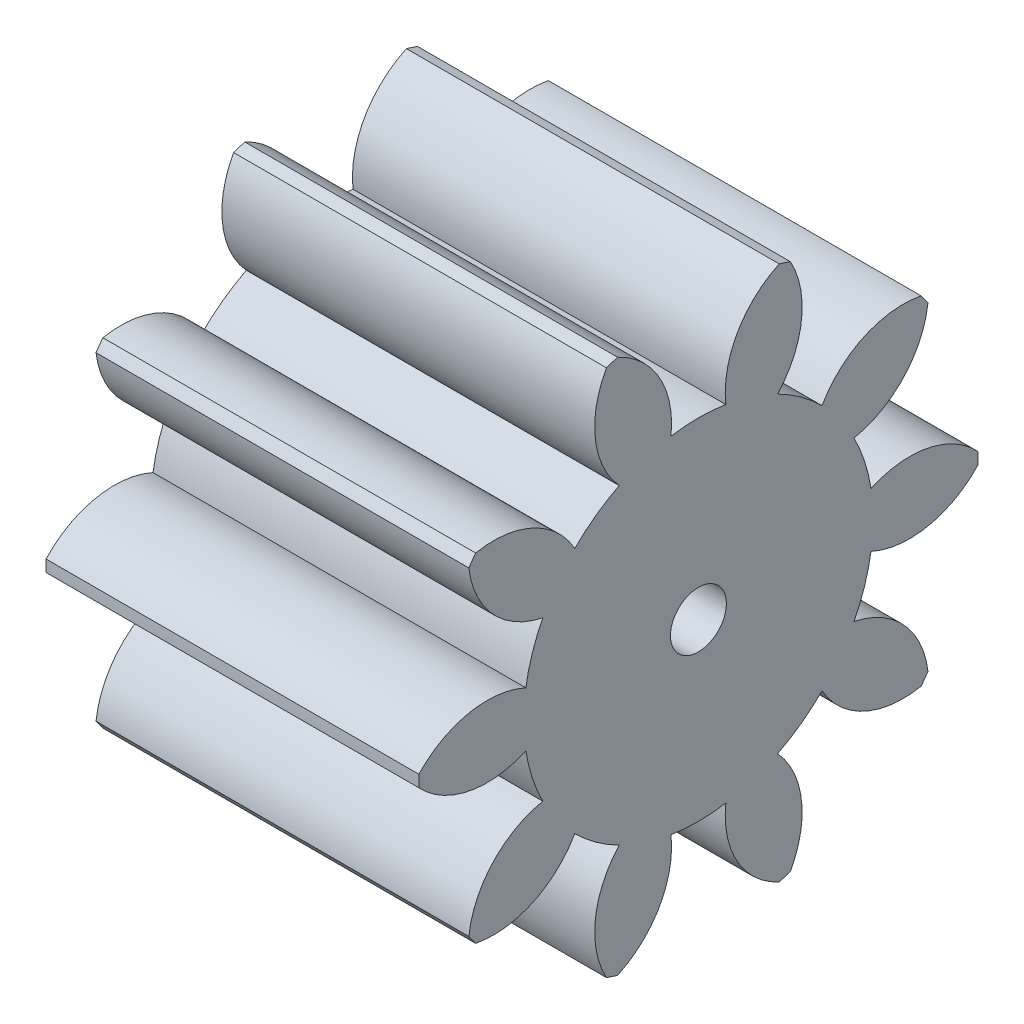
SolidWorks part; units mm, degrees
ref_plane "Plane1" through (0, 0, 0) normal (0, 0, 1) x (1, 0, 0)
ref_plane "Plane2" through (0, 0, 0) normal (0, 1, 0) x (1, 0, 0)
ref_plane "Plane3" through (0, 0, 0) normal (1, 0, 0) x (0, 0, -1)
sketch "HoldingSke" plane through (0, 0, 0) normal (0, 1, 0) x (1, 0, 0)
  line L0 (0, 0) -> (0.3939, -0.0695)
  line L1 (-15, 0) -> (100, 0) construction
  line L2 (0, 0) -> (-2.1039, 2.3779)
  line L3 (0, 0) -> (-11.863, 4.5341)
  line L4 (0, 0) -> (8.5048, 1.4996)
  line L5 (0, 0) -> (-46.8476, -17.4728)
  line L6 (0, 0) -> (-16.5793, -11.1861)
  line L7 (-2.1039, 2.3779) -> (8.6586, 51.2059)
  line L8 (-76.2, 54.61) -> (-75.7, 54.61)
  line L9 (-71.009, 38.7566) -> (-53.1078, 45.2721)
  line L10 (-76.2, 71.12) -> (104.1128, 71.12)
  line L11 (0, 0) -> (-20, 0)
  line L12 (-76.2, 101.6) -> (-76.113, 101.6)
  line L13 (24.9733, 27.94) -> (52.9518, 28.4284)
  line L14 (24.9733, 27.94) -> (24.9743, 27.94)
  line L15 (24.9733, 27.94) -> (100.4006, 29.5858)
  line L16 (-63.627, -2.5) -> (-12.827, -2.5)
  circle A0 centre (0, 0) radius 1.5
  circle A1 centre (0, 0) radius 9.374
  circle A2 centre (0, 0) radius 37.5
  circle A3 centre (0, 0) radius 1.5
  dimension "MHD" = 18.748
  dimension "Hub_dia" = 75
  dimension "Bore" = 3
  dimension "MBD" = 3
  dimension "Num_teeth" = 10
  dimension "Pitch" = 0.4
  dimension "Overall_len" = 50
  dimension "Show_teeth" = 10
  dimension "Thickness" = 20
  dimension "OAL" = 50.0001
  dimension "T_dim" = 0.5
  dimension "Ap" = 20
  dimension "H" = 19.05
  dimension "Pitch_radius" = 180.3128
  dimension "Width" = 20
  dimension "Backlash" = 0.087
  dimension "Addendum_fac" = 1
  dimension "Dedendum_fac" = 1.25
  dimension "Clearance_fac" = 0.25
  dimension "Dedendum_add" = 0.001
  dimension "Module" = 2.5
sketch "BasProSke" plane through (0, 0, 0) normal (0, 1, 0) x (1, 0, 0)
  line L0 (-10, 0) -> (60, 0) construction
  line L1 (0, 0) -> (0, 15)
  line L2 (0, 0) -> (20, 0)
  line L3 (20, 0) -> (20, 15)
  line L4 (20, 15) -> (0, 15)
  dimension "Thickness" = 20
  dimension "Diameter" = 30
revolve "Base-Revolve" add sketch "BasProSke" angle 360 about L0
sketch "TooCutSke" plane through (0, 0, 0) normal (1, 0, 0) x (0, 0, -1)
  line L1 (0, 0) -> (0, 107) construction
  line L2 (0, 0) -> (-2.1074, 12.3211) construction
  line L3 (0, 0) -> (-7.6446, 23.5277) construction
  line L4 (-2.1074, 12.3211) -> (-3.8223, 11.7639) construction
  arc A0 (1.4713, 9.2578) -> (-1.4713, 9.2578) centre (0, 0) ccw
  arc A1 (4.3702, 14.3758) -> (-4.3702, 14.3758) centre (0, 0) ccw
  circle A2 centre (0, 0) radius 12.5 construction
  circle A3 centre (0, 0) radius 11.7462 construction
  arc A4 (-1.4713, 9.2578) -> (-4.3702, 14.3758) centre (-6.4392, 9.8239) ccw
  arc A5 (4.3702, 14.3758) -> (1.4713, 9.2578) centre (6.4392, 9.8239) ccw
  dimension "Root_dia" = 18.748
  dimension "Overcut_dia" = 30.0508
  dimension "Pitch_dia" = 25
  dimension "Base_dia" = 23.4923
  dimension "Flank_rad" = 5
  dimension "Half_ang" = 18
  dimension "Half_CT" = 1.8032
extrude "ToothCut" cut sketch "TooCutSke" along normal through all
fillet "Breaks" [suppressed] radius 0.05
fillet "RootFillets" [suppressed] radius 0.626
pattern_circular "TeethCuts" count 10 every 36 about axis through (-10, 0, 0) along (1, 0, 0) of "ToothCut", "RootFillets", "Breaks"
sketch "HubNeaOneSke" plane through (0, 0, 0) normal (-1, 0, 0) x (0, 0, 1)
  circle A0 centre (0, 0) radius 9.374
  dimension "Diameter" = 18.748
extrude "HubNearOne" [suppressed] add sketch "HubNeaOneSke" along normal blind 30.0001
sketch "HubNeaBotSke" plane through (0, 0, 0) normal (-1, 0, 0) x (0, 0, 1)
  circle A0 centre (0, 0) radius 9.374
  dimension "Diameter" = 18.748
extrude "HubNearBoth" [suppressed] add sketch "HubNeaBotSke" along normal blind 15
ref_plane "FarPln" through (20, 0, 0) normal (1, 0, 0) x (0, 0, -1)
sketch "HubFarSke" plane through (20, 0, 0) normal (1, 0, 0) x (0, 0, -1)
  circle A0 centre (0, 0) radius 9.374
  dimension "Diameter" = 18.748
extrude "HubFar" [suppressed] add sketch "HubFarSke" along normal blind 15
sketch "BorSke" plane through (0, 0, 0) normal (1, 0, 0) x (0, 0, -1)
  circle A0 centre (0, 0) radius 1.5
  dimension "Diameter" = 3
extrude "Bore" cut sketch "BorSke" along normal mid plane 100.0001
sketch "KeySke" plane through (0, 0, 0) normal (1, 0, 0) x (0, 0, -1)
  line L0 (-0.6, 0) -> (-0.6, 2)
  line L1 (-0.6, 2) -> (0.6, 2)
  line L2 (0.6, 2) -> (0.6, 0)
  line L3 (0, 0) -> (0, 34) construction
  line L4 (-0.6, 0) -> (0.6, 0)
  dimension "Offset" = 2
  dimension "Width" = 1.2
extrude "Keyway" [suppressed] cut sketch "KeySke" along normal mid plane 100.0001
pattern_circular "Keyway2" [suppressed] count 2 every 90 about axis through (-10, 0, 0) along (1, 0, 0)
equation "' \"Module@HoldingSke\" = 6.35"
equation "' \"Num_teeth@HoldingSke\" = 12"
equation "' \"Ap@HoldingSke\" =  20"
equation "' \"Ap@HoldingSke\" = 20"
equation "' \"Width@HoldingSke\" = 0.5 * 25.4"
equation "' \"Hub_dia@HoldingSke\"= 1 * 25.4"
equation "' \"Hub_dia@HoldingSke\" = 1 * 25.4"
equation "' \"Overall_len@HoldingSke\" = 1.0 * 25.4"
equation "' \"Bore@HoldingSke\" = 0.75 * 25.4"
equation "' \"T_dim@HoldingSke\" = 0.1 * 25.4"
equation "' \"Width@KeySke\" = 0.25 * 25.4"
equation "' \"Show_teeth@HoldingSke\" = 13"
equation "' \"Backlash@HoldingSke\" = 0.009 * 25.4"
equation "' \"Addendum_fac@HoldingSke\" = 1.0"
equation "' \"Dedendum_fac@HoldingSke\" = 1.25"
equation "' \"Dedendum_add@HoldingSke\" = 0.00005 * 25.4"
equation "' \"Clearance_fac@HoldingSke\" = 0.25"
equation "\"Pitch@HoldingSke\" = 1 / \"Module@HoldingSke\""
equation "\"Overcut_dia@TooCutSke\" = (\"Num_teeth@HoldingSke\" + 2 * \"Addendum_fac@HoldingSke\") / \"Pitch@HoldingSke\" + 0.002 * 25.4"
equation "\"Pitch_dia@TooCutSke\" = \"Num_teeth@HoldingSke\" / \"Pitch@HoldingSke\""
equation "\"Base_dia@TooCutSke\" = \"Num_teeth@HoldingSke\" / \"Pitch@HoldingSke\" * cos((\"Ap@HoldingSke\"  * 3.14159265 / 180))"
equation "\"Root_dia@TooCutSke\" = (\"Num_teeth@HoldingSke\" + 2) / \"Pitch@HoldingSke\" - 2 * (\"Addendum_fac@HoldingSke\" + \"Dedendum_fac@HoldingSke\") / \"Pitch@HoldingSke\" - \"Dedendum_add@HoldingSke\" * 2"
equation "\"Half_ang@TooCutSke\" = 180 / \"Num_teeth@HoldingSke\""
equation "\"Half_CT@TooCutSke\" = \"Num_teeth@HoldingSke\" / \"Pitch@HoldingSke\" * sin((3.14159265 / 2 / \"Num_teeth@HoldingSke\")) / 2 - 7 * \"Backlash@HoldingSke\" / 4"
equation "\"Flank_rad@TooCutSke\" = \"Num_teeth@HoldingSke\" / \"Pitch@HoldingSke\" / 5"
equation "\"Radius@RootFillets\" = \"Clearance_fac@HoldingSke\" / \"Pitch@HoldingSke\" + \"Dedendum_add@HoldingSke\""
equation "\"Break_rad@Breaks\" = 0.02 / \"Pitch@HoldingSke\""
equation "\"Thickness@HoldingSke\" = \"Width@HoldingSke\""
equation "\"OAL@HoldingSke\" = \"Thickness@HoldingSke\""
equation "\"MHD@HoldingSke\" = (\"Num_teeth@HoldingSke\" + 2) / \"Pitch@HoldingSke\" - 2 * (\"Addendum_fac@HoldingSke\" + \"Dedendum_fac@HoldingSke\")  / \"Pitch@HoldingSke\" - \"Dedendum_add@HoldingSke\" * 2"
equation "\"MBD@HoldingSke\" = (\"Num_teeth@HoldingSke\" + 2) / \"Pitch@HoldingSke\" - 2 * (\"Addendum_fac@HoldingSke\" + \"Dedendum_fac@HoldingSke\")  / \"Pitch@HoldingSke\" - \"Dedendum_add@HoldingSke\" * 2 - 0.002 * 25.4"
equation "\"MHD@HoldingSke\" = ((sgn( \"MHD@HoldingSke\" - \"Hub_dia@HoldingSke\" )-1)*( \"MHD@HoldingSke\" - \"Hub_dia@HoldingSke\" ))/-2+ \"Hub_dia@HoldingSke\""
equation "\"MBD@HoldingSke\" = ((sgn( \"MBD@HoldingSke\" - \"Bore@HoldingSke\" )-1)*( \"MBD@HoldingSke\" - \"Bore@HoldingSke\" ))/-2+ \"Bore@HoldingSke\""
equation "\"OAL@HoldingSke\" = ((sgn( \"OAL@HoldingSke\" - \"Overall_len@HoldingSke\" )+1)*( \"OAL@HoldingSke\" - \"Overall_len@HoldingSke\" ))/2 + \"Overall_len@HoldingSke\" + 0.000002 * 25.4"
equation "\"Num_teeth@TeethCuts\" = int( \"Show_teeth@HoldingSke\" ) + 1"
equation "\"Num_teeth@TeethCuts\" = ((sgn( \"Num_teeth@TeethCuts\" - \"Num_teeth@HoldingSke\" )-1)*( \"Num_teeth@TeethCuts\" - \"Num_teeth@HoldingSke\" ))/-2+ \"Num_teeth@HoldingSke\""
equation "\"Num_teeth@TeethCuts\" = ((sgn( \"Num_teeth@TeethCuts\" - 2.0)+1)*( \"Num_teeth@TeethCuts\" - 2.0))/2 +2.0"
equation "\"Angle@TeethCuts\" = 360.0 / \"Num_teeth@HoldingSke\""
equation "\"Diameter@BasProSke\" = (\"Num_teeth@HoldingSke\" + 2 * \"Addendum_fac@HoldingSke\") / \"Pitch@HoldingSke\""
equation "\"Thickness@BasProSke\"  = \"Thickness@HoldingSke\""
equation "' \"Fillet_rad@BasProSke\" =  \"Thickness@HoldingSke\" * 0.05"
equation "' \"Fillet_rad@BasProSke\" = \"Thickness@HoldingSke\" * 0.05"
equation "\"MHD@HoldingSke\" = ((sgn( \"MHD@HoldingSke\" - \"Root_dia@TooCutSke\" )-1)*( \"MHD@HoldingSke\" - \"Root_dia@TooCutSke\" ))/-2+ \"Root_dia@TooCutSke\""
equation "\"Diameter@HubNeaOneSke\" = \"MHD@HoldingSke\""
equation "\"Length@HubNearOne\" = \"OAL@HoldingSke\" - \"Thickness@BasProSke\""
equation "\"Diameter@HubNeaBotSke\" = \"MHD@HoldingSke\""
equation "\"Length@HubNearBoth\" = ( \"OAL@HoldingSke\" - \"Thickness@BasProSke\" ) / 2.0"
equation "\"Thickness@FarPln\" = \"Thickness@BasProSke\""
equation "\"Diameter@HubFarSke\" = \"MHD@HoldingSke\""
equation "\"Length@HubFar\" = ( \"OAL@HoldingSke\" - \"Thickness@BasProSke\" ) / 2.0"
equation "\"Diameter@BorSke\" = \"MBD@HoldingSke\""
equation "\"D1@Bore\" = \"OAL@HoldingSke\" * 2.0"
equation "\"D1@Keyway\" = \"OAL@HoldingSke\" * 2.0"
equation "\"Offset@KeySke\" = \"T_dim@HoldingSke\" + \"MBD@HoldingSke\" / 2.0"
